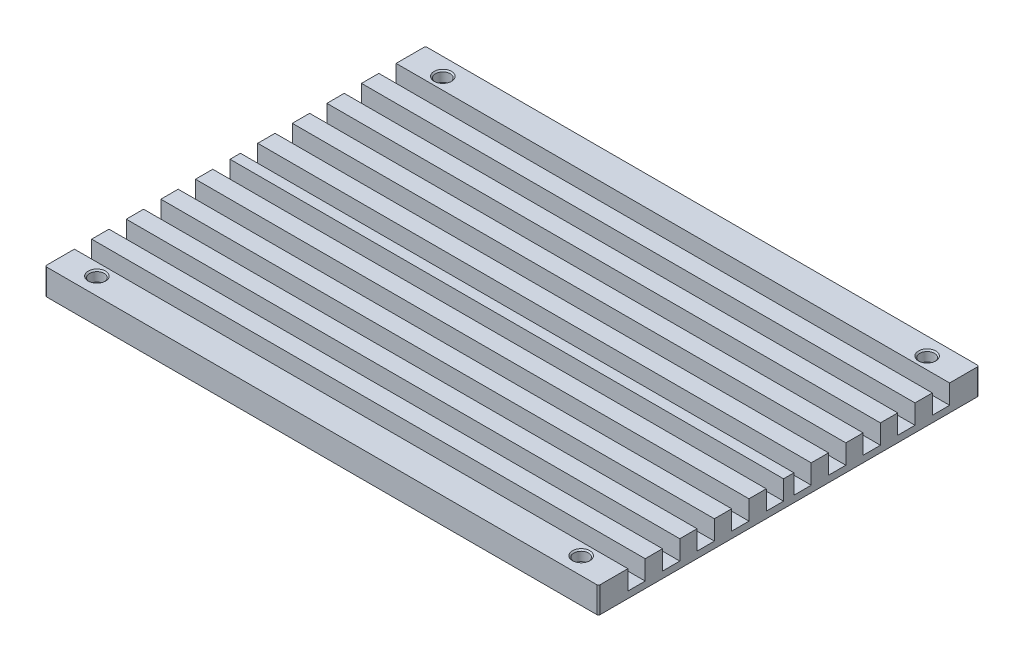
SolidWorks part; units mm, degrees
ref_plane "Front Plane" through (0, 0, 0) normal (0, 0, 1) x (1, 0, 0)
ref_plane "Top Plane" through (0, 0, 0) normal (0, 1, 0) x (1, 0, 0)
ref_plane "Right Plane" through (0, 0, 0) normal (1, 0, 0) x (0, 0, -1)
sketch "Sketch1" plane through (0, 0, 0) normal (0, 1, 0) x (1, 0, 0)
  line L1 (160, -110) -> (-160, -110)
  line L2 (160, -110) -> (160, 110)
  line L3 (160, 110) -> (-160, 110)
  line L4 (-160, -110) -> (-160, 110)
  line L5 (160, -110) -> (-160, 110) construction
  line L6 (160, 110) -> (-160, -110) construction
  point P0 (0, 0)
  dimension "D1" = 320
  dimension "D2" = 220
extrude "Boss-Extrude1" add sketch "Sketch1" along normal blind 15
fillet "Fillet2" radius 1 4 edges at (-160, 7.5, -110) (-160, 7.5, 110) (160, 7.5, -110) (160, 7.5, 110)
sketch "Sketch3" plane through (0, 15, 0) normal (0, 1, 0) x (1, 0, 0)
  line L0 (0, 0) -> (-184.4799, 0) construction
  line L1 (0, 0) -> (203.3345, 0) construction
  line L2 (-160, 0) -> (-160, 40) construction
  line L3 (-160, 109) -> (-160, -109) construction
  line L4 (-160, 40) -> (-140, 40) construction
  line L5 (-160, 40) -> (-160, 100) construction
  line L6 (-160, 100) -> (-140, 100) construction
  line L7 (0, 0) -> (0, 137.5501) construction
  line L8 (0, 0) -> (0, -133.0696) construction
  point P9 (-140, -40)
  point P12 (-140, -100)
  point P15 (140, -100)
  point P16 (140, -40)
  point P17 (140, 40)
  point P18 (140, 100)
  dimension "D1" = 40
  dimension "D2" = 20
  dimension "D3" = 60
hole_wizard "CBORE for M5 Hex Socket Head Cap Screw2" positions "3DSketch2" profile "Sketch5" counterbore size "M5" standard "ISO" end condition through all
sketch3d "3DSketch2"
  point P0 (-140, 15, -100)
  point P9 (-140, 15, 100)
  point P12 (140, 15, 100)
  point P21 (140, 15, -100)
sketch "Sketch5" plane through (-140, 15, -100) normal (1, 0, 0) x (0, 0, 1)
  line L0 (0, 0) -> (0, 15)
  line L1 (0, 15) -> (2.75, 15)
  line L3 (2.75, 15) -> (2.75, 6)
  line L4 (4.25, 6) -> (2.75, 6)
  line L5 (4.25, 6) -> (4.25, 0.775)
  line L6 (4.25, 0.775) -> (5.025, 0)
  line L7 (5.025, 0) -> (0, 0)
  line L8 (-4.25, 0.775) -> (-5.025, 0) construction
  line L11 (0, -6.35) -> (0, 107.95) construction
  dimension "Thru Hole Dia." = 5.5
  dimension "Thru Hole Depth" = 15
  dimension "C'Bore Dia." = 8.5
  dimension "C'Bore Depth" = 6
  dimension "Near C'Sink Dia." = 10.05
  dimension "Near C'Sink Angle" = 90
sketch "Sketch6" plane through (0, 15, 0) normal (0, 1, 0) x (1, 0, 0)
  line L0 (159, 110) -> (-159, 110) construction
  line L1 (-130, 108.0965) -> (-130, 80) construction
  line L2 (-153.4678, 80) -> (-164.2629, 80) construction
  line L3 (-153.4678, 80) -> (191.0416, 80) construction
  line L4 (-160, 109) -> (-160, -109) construction
  line L5 (0, 0) -> (-191.0125, 0) construction
  line L6 (-130, 108.0965) -> (-130, 115.2474) construction
  line L7 (-130, 110) -> (-80, 110) construction
  line L8 (-80, 110) -> (-80, 80) construction
  line L9 (-80, 110) -> (-30, 110)
  line L10 (-30, 110) -> (-30, 80)
  line L11 (-30, 110) -> (30, 110) construction
  line L12 (30, 110) -> (30, 80) construction
  line L13 (30, 110) -> (80, 110) construction
  line L14 (80, 110) -> (80, 80) construction
  line L15 (80, 110) -> (130, 110) construction
  line L16 (130, 110) -> (130, 80) construction
  line L17 (0, 0) -> (193.4125, 0) construction
  line L18 (-130, 80) -> (-130, 0) construction
  line L19 (-80, 80) -> (-80, 0) construction
  line L20 (-30, 80) -> (-30, 0) construction
  line L21 (30, 80) -> (30, 0) construction
  line L22 (80, 80) -> (80, 0) construction
  line L23 (130, 80) -> (130, 0) construction
  point P24 (130, -80)
  point P26 (80, -80)
  point P27 (30, -80)
  point P28 (-30, -80)
  point P29 (-80, -80)
  point P30 (-130, -80)
  dimension "D1" = 30
  dimension "D2" = 30
  dimension "D3" = 50
  dimension "D4" = 50
  dimension "D5" = 60
  dimension "D6" = 50
  dimension "D7" = 50
sketch "Sketch7" plane through (-160, 0, 0) normal (-1, 0, 0) x (0, 0, 1)
  line L0 (0, 0) -> (0, 29.1523) construction
  line L1 (-110, 7.5) -> (0, 7.5) construction
  line L2 (-110, 0) -> (-110, 15) construction
  line L3 (-109, 15) -> (109, 15) construction
  line L4 (-93, 15) -> (-83, 15)
  line L5 (-93, 15) -> (-93, 3.796)
  line L6 (-93, 3.796) -> (-83, 3.796)
  line L7 (-83, 15) -> (-83, 3.796)
  line L8 (13, 3.796) -> (3, 3.796)
  line L9 (-73, 15) -> (-63, 15)
  line L10 (-73, 15) -> (-73, 3.796)
  line L11 (-73, 3.796) -> (-63, 3.796)
  line L12 (-63, 15) -> (-63, 3.796)
  line L13 (-53, 15) -> (-43, 15)
  line L14 (-53, 15) -> (-53, 3.796)
  line L15 (-53, 3.796) -> (-43, 3.796)
  line L16 (-43, 15) -> (-43, 3.796)
  line L17 (-33, 15) -> (-23, 15)
  line L18 (-33, 15) -> (-33, 3.796)
  line L19 (-33, 3.796) -> (-23, 3.796)
  line L20 (-23, 15) -> (-23, 3.796)
  line L21 (-13, 15) -> (-3, 15)
  line L22 (-13, 15) -> (-13, 3.796)
  line L23 (-13, 3.796) -> (-3, 3.796)
  line L24 (-3, 15) -> (-3, 3.796)
  line L25 (3, 15) -> (3, 3.796)
  line L26 (13, 15) -> (3, 15)
  line L27 (13, 15) -> (13, 3.796)
  line L28 (33, 3.796) -> (23, 3.796)
  line L29 (23, 15) -> (23, 3.796)
  line L30 (33, 15) -> (23, 15)
  line L31 (33, 15) -> (33, 3.796)
  line L32 (53, 3.796) -> (43, 3.796)
  line L33 (43, 15) -> (43, 3.796)
  line L34 (53, 15) -> (43, 15)
  line L35 (53, 15) -> (53, 3.796)
  line L36 (73, 3.796) -> (63, 3.796)
  line L37 (63, 15) -> (63, 3.796)
  line L38 (73, 15) -> (63, 15)
  line L39 (73, 15) -> (73, 3.796)
  line L40 (93, 3.796) -> (83, 3.796)
  line L41 (83, 15) -> (83, 3.796)
  line L42 (93, 15) -> (83, 15)
  line L43 (93, 15) -> (93, 3.796)
  point P25 (-63, 9.398)
  dimension "D1" = 10
  dimension "D2" = 10
  dimension "D3" = 10
  dimension "D4" = 10
  dimension "D5" = 17
  dimension "D6" = 10
  dimension "D7" = 10
  dimension "D8" = 10
  dimension "D9" = 10
  dimension "D10" = 10
extrude "Cut-Extrude1" cut sketch "Sketch7" against normal through all
